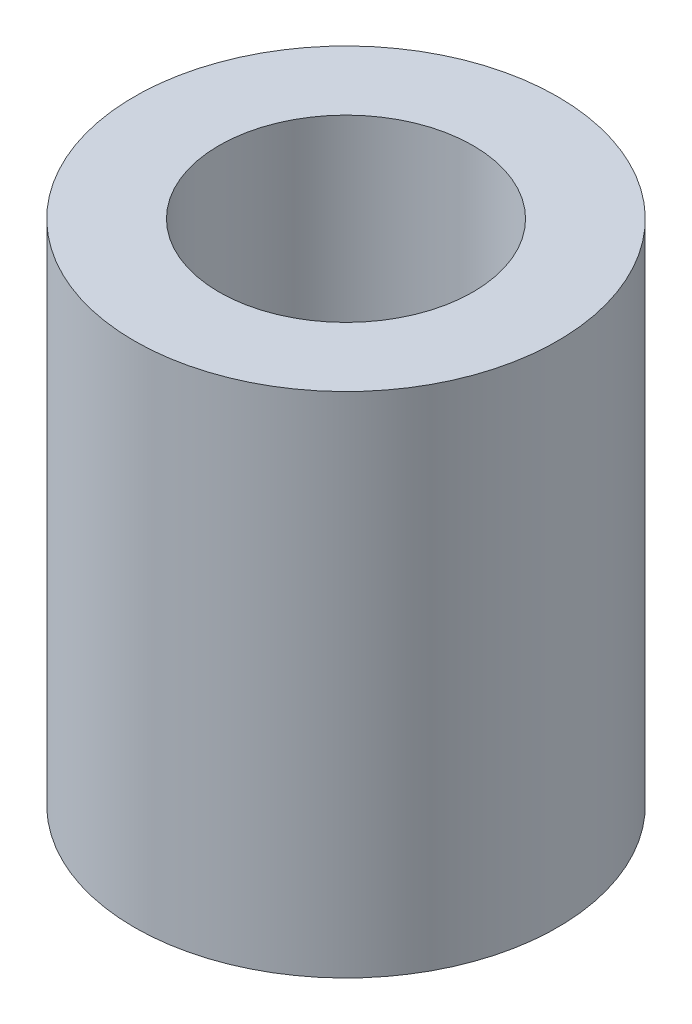
SolidWorks part; units mm, degrees
ref_plane "Front Plane" through (0, 0, 0) normal (0, 0, 1) x (1, 0, 0)
ref_plane "Top Plane" through (0, 0, 0) normal (0, 1, 0) x (1, 0, 0)
ref_plane "Right Plane" through (0, 0, 0) normal (1, 0, 0) x (0, 0, -1)
sketch "Sketch1" plane through (0, 0, 0) normal (0, 1, 0) x (1, 0, 0)
  circle A0 centre (0, 0) radius 1.5
  circle A1 centre (0, 0) radius 2.5
  dimension "D1" = 5
  dimension "D2" = 3
extrude "Boss-Extrude1" add sketch "Sketch1" along normal blind 6
